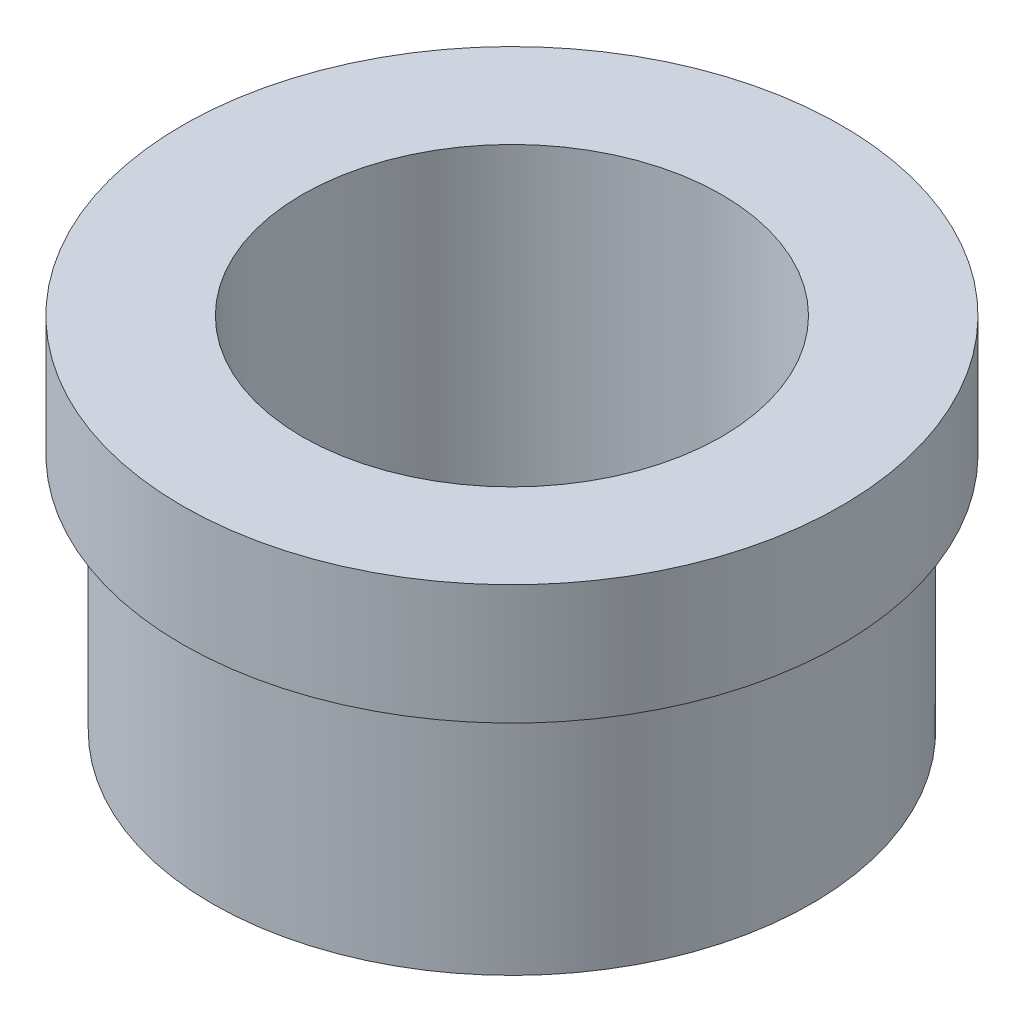
SolidWorks part; units mm, degrees
ref_plane "Front Plane" through (0, 0, 0) normal (0, 0, 1) x (1, 0, 0)
ref_plane "Top Plane" through (0, 0, 0) normal (0, 1, 0) x (1, 0, 0)
ref_plane "Right Plane" through (0, 0, 0) normal (1, 0, 0) x (0, 0, -1)
sketch "Sketch1" plane through (0, 0, 0) normal (0, 1, 0) x (1, 0, 0)
  circle A0 centre (0, 0) radius 25
  circle A1 centre (0, 0) radius 17.5
  dimension "D1" = 35
  dimension "D2" = 50
extrude "Boss-Extrude1" add sketch "Sketch1" along normal blind 20
sketch "Sketch2" plane through (0, 20, 0) normal (0, 1, 0) x (1, 0, 0)
  circle A0 centre (0, 0) radius 27.5
  circle A1 centre (0, 0) radius 17.5
  dimension "D1" = 55
  dimension "D2" = 35
extrude "Boss-Extrude2" add sketch "Sketch2" along normal blind 10
